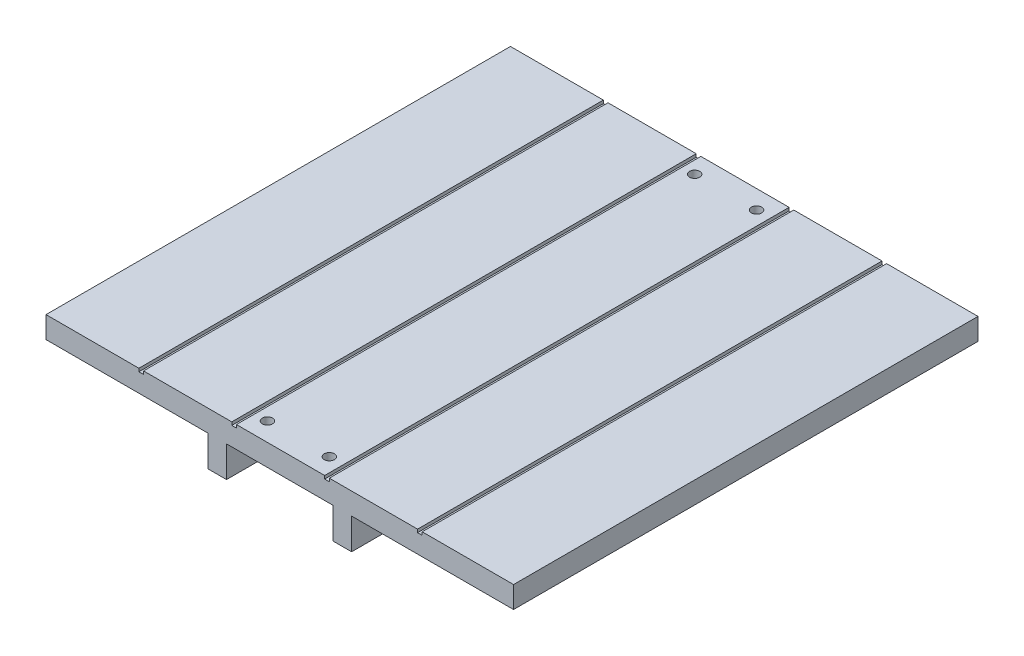
SolidWorks part; units mm, degrees
ref_plane "Front Plane" through (0, 0, 0) normal (0, 0, 1) x (1, 0, 0)
ref_plane "Top Plane" through (0, 0, 0) normal (0, 1, 0) x (1, 0, 0)
ref_plane "Right Plane" through (0, 0, 0) normal (1, 0, 0) x (0, 0, -1)
sketch "Sketch1" plane through (0, 0, 0) normal (0, 0, 1) x (1, 0, 0)
  line L0 (0, 3.5) -> (0, -3.5) construction
  line L1 (-75.5, 3.5) -> (75.5, 3.5)
  line L2 (-75.5, 3.5) -> (-75.5, -3.5)
  line L3 (-75.5, -3.5) -> (-23.2, -3.5)
  line L4 (75.5, 3.5) -> (75.5, -3.5)
  line L5 (-75.5, 3.5) -> (75.5, -3.5) construction
  line L6 (-75.5, -3.5) -> (75.5, 3.5) construction
  line L7 (17.2, -3.5) -> (17.2, -13.5)
  line L8 (17.2, -13.5) -> (23.2, -13.5)
  line L9 (23.2, -13.5) -> (23.2, -3.5)
  line L10 (-23.2, -13.5) -> (-23.2, -3.5)
  line L11 (-17.2, -13.5) -> (-23.2, -13.5)
  line L12 (-17.2, -3.5) -> (-17.2, -13.5)
  line L13 (-17.2, -3.5) -> (17.2, -3.5)
  line L14 (23.2, -3.5) -> (75.5, -3.5)
  point P0 (0, 0)
  dimension "D1" = 7
  dimension "D2" = 151
  dimension "D3" = 6
  dimension "D4" = 10
  dimension "D5" = 23.2
  dimension "D6" = 34.4
extrude "Boss-Extrude1" add sketch "Sketch1" along normal blind 150
sketch "Sketch4" plane through (0, -3.5, 0) normal (0, -1, 0) x (1, 0, 0)
  line L0 (0, 150) -> (0, 0) construction
  line L1 (-17.2, 150) -> (17.2, 150) construction
  line L2 (-17.2, 144) -> (17.2, 144) construction
  line L3 (-17.2, 150) -> (-17.2, 0) construction
  line L4 (17.2, 150) -> (17.2, 0) construction
  line L5 (-17.2, 6) -> (17.2, 6) construction
  line L6 (-10, 150) -> (-10, 0) construction
  line L7 (-17.2, 0) -> (17.2, 0) construction
  line L8 (10, 150) -> (10, 0) construction
  circle A0 centre (-10, 6) radius 1.65
  circle A1 centre (10, 6) radius 1.65
  circle A2 centre (-10, 144) radius 1.65
  circle A3 centre (10, 144) radius 1.65
  dimension "D4" = 3.3
  dimension "D5" = 3.3
  dimension "D1" = 6
  dimension "D2" = 6
  dimension "D3" = 10
extrude "Cut-Extrude1" cut sketch "Sketch4" against normal up to surface (7 mm away) up to face at (0, 3.5, 75)
sketch "Sketch5" plane through (0, 3.5, 0) normal (0, 1, 0) x (1, 0, 0)
  line L0 (75.5, 0) -> (-75.5, 0) construction
  line L1 (-45.5, 0) -> (-44, 0)
  line L2 (-45.5, 0) -> (-45.5, -150)
  line L3 (-45.5, -150) -> (-44, -150)
  line L4 (-44, 0) -> (-44, -150)
  line L5 (75.5, -150) -> (-75.5, -150) construction
  line L6 (-75.5, -150) -> (-75.5, 0) construction
  line L7 (-15.5, 0) -> (-15.5, -150)
  line L8 (-15.5, 0) -> (-14, 0)
  line L9 (-14, 0) -> (-14, -150)
  line L10 (-15.5, -150) -> (-14, -150)
  line L11 (14.5, 0) -> (14.5, -150)
  line L12 (14.5, 0) -> (16, 0)
  line L13 (16, 0) -> (16, -150)
  line L14 (14.5, -150) -> (16, -150)
  line L15 (44.5, 0) -> (44.5, -150)
  line L16 (44.5, 0) -> (46, 0)
  line L17 (46, 0) -> (46, -150)
  line L18 (44.5, -150) -> (46, -150)
  dimension "D1" = 1.5
  dimension "D2" = 30
  dimension "D3" = 4
extrude "Cut-Extrude2" cut sketch "Sketch5" against normal blind 1
